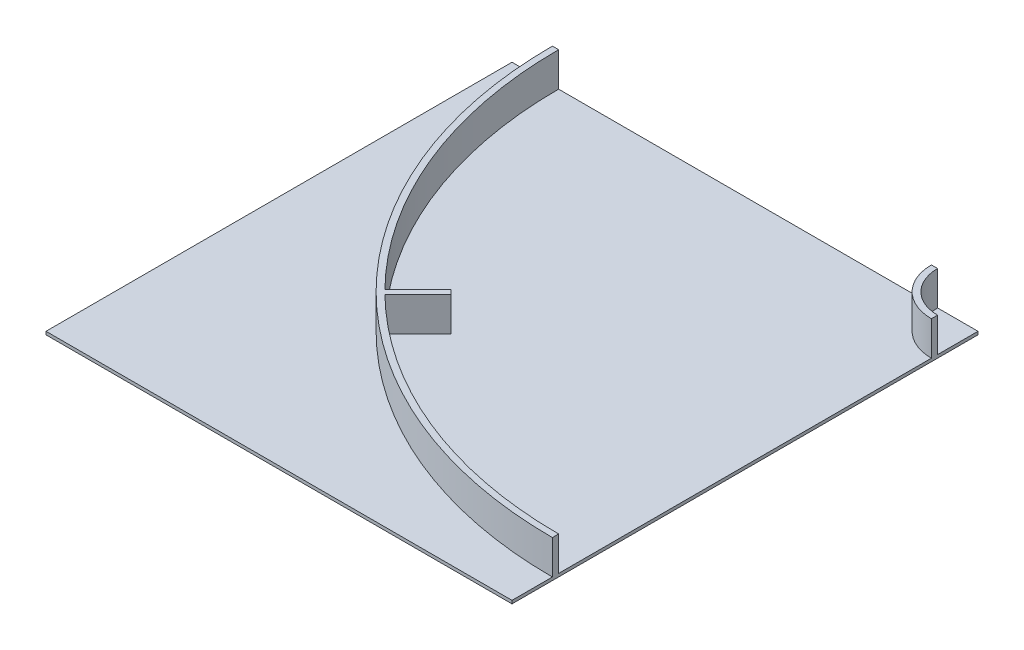
SolidWorks part; units mm, degrees
ref_plane "Front Plane" through (0, 0, 0) normal (0, 0, 1) x (1, 0, 0)
ref_plane "Top Plane" through (0, 0, 0) normal (0, 1, 0) x (1, 0, 0)
ref_plane "Right Plane" through (0, 0, 0) normal (1, 0, 0) x (0, 0, -1)
sketch "Sketch2" plane through (0, 0, 0) normal (0, 1, 0) x (1, 0, 0)
  line L1 (-750, 750) -> (750, 750)
  line L2 (-750, 750) -> (-750, -750)
  line L3 (-750, -750) -> (750, -750)
  line L4 (750, 750) -> (750, -750)
  line L5 (-750, 750) -> (750, -750) construction
  line L6 (-750, -750) -> (750, 750) construction
  point P0 (0, 0)
  dimension "D1" = 1500
  dimension "D2" = 1500
extrude "Boss-Extrude1" add sketch "Sketch2" along normal blind 10
sketch "Sketch3" plane through (0, 10, 0) normal (0, 1, 0) x (1, 0, 0)
  line L0 (620, 750) -> (620, -750) construction
  line L1 (750, 750) -> (-750, 750) construction
  line L2 (-750, -750) -> (750, -750) construction
  line L3 (600, 750) -> (600, -750) construction
  line L4 (750, -750) -> (750, 750) construction
  line L5 (-750, -600) -> (750, -600) construction
  line L6 (-750, 750) -> (-750, -750) construction
  line L7 (-750, -620) -> (750, -620) construction
  line L8 (-750, 0) -> (750, 0) construction
  line L9 (0, 750) -> (0, -750) construction
  line L10 (-750, 620) -> (750, 620) construction
  line L11 (-750, 600) -> (750, 600) construction
  line L12 (-620, 750) -> (-620, -750) construction
  line L13 (-600, 750) -> (-600, -750) construction
  circle A0 centre (750, 750) radius 150
  circle A1 centre (750, 750) radius 1350
  circle A2 centre (750, 750) radius 130
  circle A3 centre (750, 750) radius 1370
  line M3 (750, -750) -> (750, 750)
  line M4 (750, 750) -> (-750, 750)
  dimension "D6" = 150
  dimension "D5" = 20
  dimension "D7" = 20
  dimension "D8" = 150
extrude "Boss-Extrude2" add sketch "Sketch3" along normal blind 110 contours A3 A1 M4 M3 | A2 A0 M4 M3
sketch "Sketch4" plane through (0, 10, 0) normal (0, 1, 0) x (1, 0, 0)
  line L0 (750, 750) -> (-750, -750) construction
  line L1 (-197.5231, -211.6652) -> (-91.4571, -105.5992)
  line L2 (-197.5231, -211.6652) -> (-211.6652, -197.5231)
  line L3 (-91.4571, -105.5992) -> (-105.5992, -91.4571)
  line L4 (-211.6652, -197.5231) -> (-105.5992, -91.4571)
  line L5 (-197.5231, -211.6652) -> (-105.5992, -91.4571) construction
  line L6 (-91.4571, -105.5992) -> (-211.6652, -197.5231) construction
  line L7 (-98.5281, -98.5281) -> (-204.5942, -204.5942) construction
  arc A0 (-600, 750) -> (750, -600) centre (750, 750) ccw construction
  point P5 (-151.5611, -151.5611)
  dimension "D1" = 20
extrude "Boss-Extrude3" add sketch "Sketch4" along normal up to surface (110 mm away) up to face at (665.5025, 120, -665.5025)
equation "\"CellSize\"=1500"
equation "\"D1@Sketch2\"=\"CellSize\""
equation "\"D2@Sketch2\"=\"CellSize\""
equation "\"TrackWidth\"= 1200"
equation "\"C\"=342.079"
equation "\"WallWidth\"=20"
equation "\"D6@Sketch3\"=\"EdgeWidth\""
equation "\"D5@Sketch3\"=\"WallWidth\""
equation "\"D7@Sketch3\"=\"WallWidth\""
equation "\"EdgeWidth\"= ( \"CellSize\" - \"TrackWidth\" ) / 2"
equation "\"D8@Sketch3\"=\"EdgeWidth\""
equation "\"D1@Sketch4\"=\"WallWidth\""
